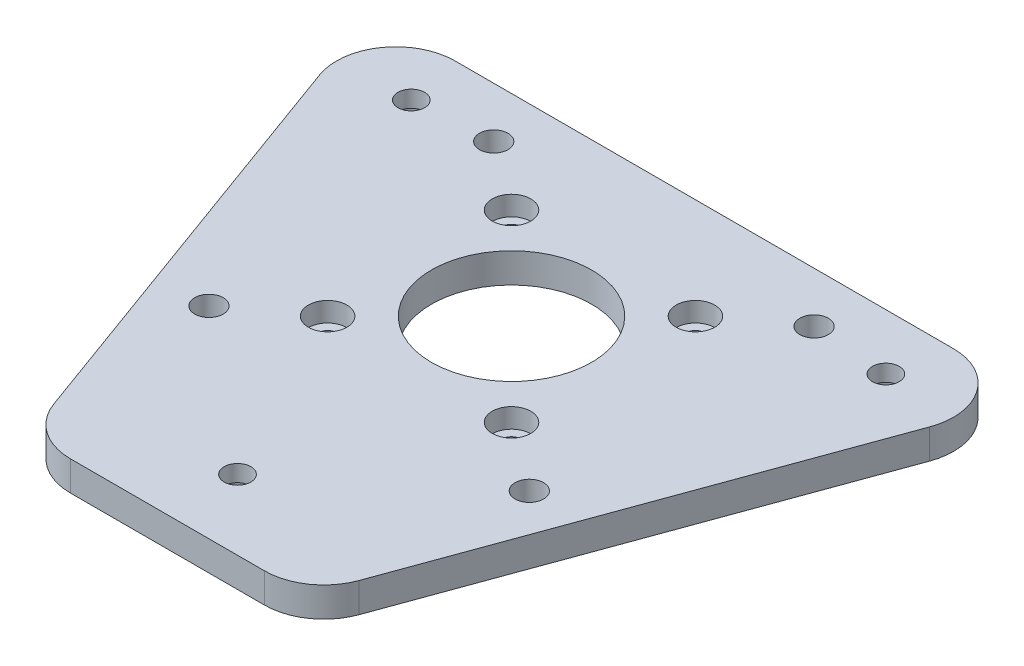
SolidWorks part; units mm, degrees
material "Nylon 101"
ref_plane "Front Plane" through (0, 0, 0) normal (0, 0, 1) x (1, 0, 0)
ref_plane "Top Plane" through (0, 0, 0) normal (0, 1, 0) x (1, 0, 0)
ref_plane "Right Plane" through (0, 0, 0) normal (1, 0, 0) x (0, 0, -1)
sketch "Sketch2" plane through (0, 0, 0) normal (0, 1, 0) x (1, 0, 0)
  line L1 (-65, -65) -> (65, -65)
  line L2 (-65, -65) -> (-65, 65)
  line L3 (-65, 65) -> (65, 65)
  line L4 (65, -65) -> (65, 65)
  line L5 (-65, -65) -> (65, 65) construction
  line L6 (-65, 65) -> (65, -65) construction
  point P0 (0, 0)
  dimension "D1" = 130
  dimension "D2" = 130
extrude "Boss-Extrude1" add sketch "Sketch2" along normal blind 5
ref_plane "Plane1" through (0, 5, 0) normal (0, 1, 0) x (1, 0, 0)
sketch "Sketch3" plane through (0, 5, 0) normal (0, 1, 0) x (1, 0, 0)
  line L0 (0, 0) -> (0, 15.5) construction
  line L1 (0, 15.5) -> (-15.5, 15.5) construction
  line L2 (0, 0) -> (-27, 0) construction
  line L3 (0, 0) -> (0, -24) construction
  circle A0 centre (0, 0) radius 13.5
  point P17 (-27, -24)
  point P18 (27, -24)
  point P25 (15.5, -15.5)
  point P26 (-15.5, -15.5)
  point P27 (-15.5, 15.5)
  point P28 (-27, 24)
  point P29 (27, 24)
  point P30 (15.5, 15.5)
  dimension "D1" = 27
  dimension "D4" = 15.5
  dimension "D9" = 15.5
  dimension "D2" = 15.5
  dimension "D3" = 15.5
  dimension "D6" = 27
  dimension "D7" = 54
  dimension "D8" = 24
  dimension "D5" = 48
  dimension "D10" = 27
  dimension "D11" = 24
extrude "Cut-Extrude1" cut sketch "Sketch3" against normal blind 5
ref_plane "Plane3" through (0, 5, 0) normal (0, 1, 0) x (1, 0, 0)
sketch "Sketch5" plane through (0, 0, 0) normal (0, 1, 0) x (1, 0, 0)
  line L0 (0, 0) -> (-40, 0) construction
  line L1 (-40, 0) -> (-40, 23.1) construction
  line L2 (0, 0) -> (0, -18.9982) construction
  point P11 (0, -46.19)
  point P12 (-40, 23.1)
  point P13 (40, 23.1)
  dimension "D3" = 46.19
  dimension "D1" = 23.1
  dimension "D2" = 40
  dimension "D4" = 40
ref_plane "Plane6" through (0, 5, 0) normal (0, 1, 0) x (1, 0, 0)
sketch "Sketch8" plane through (0, 5, 0) normal (0, 1, 0) x (1, 0, 0)
  line L0 (0, 0) -> (0, 30.6481) construction
  line L1 (0, 0) -> (56.2917, 32.5) construction
  line L2 (0, 0) -> (37.3839, 0) construction
  line L3 (0, 0) -> (-56.2917, 32.5) construction
  line L4 (0, 0) -> (0, -58) construction
  line L5 (-42.0098, 32.5) -> (42.0098, 32.5)
  line L6 (51.4067, 19.0796) -> (25.7449, -51.4204)
  line L7 (-51.4067, 19.0796) -> (-25.7449, -51.4204)
  line L8 (-16.3481, -58) -> (16.3481, -58)
  line L9 (-65, 65) -> (-65, -65)
  line L10 (-65, -65) -> (65, -65)
  line L11 (65, -65) -> (65, 65)
  line L12 (65, 65) -> (-65, 65)
  arc A0 (-25.7449, -51.4204) -> (-16.3481, -58) centre (-16.3481, -48) ccw
  arc A1 (25.7449, -51.4204) -> (16.3481, -58) centre (16.3481, -48) cw
  arc A2 (51.4067, 19.0796) -> (42.0098, 32.5) centre (42.0098, 22.5) ccw
  arc A3 (-51.4067, 19.0796) -> (-42.0098, 32.5) centre (-42.0098, 22.5) cw
  point P9 (0, -58)
  point P14 (-23.35, -58)
  point P17 (23.35, -58)
  dimension "D5" = 10
  dimension "D1" = 30
  dimension "D2" = 65
  dimension "D3" = 58
  dimension "D4" = 46.7
extrude "Cut-Extrude6" cut sketch "Sketch8" against normal through all
hole_wizard "M4 Clearance Hole1" positions "Sketch11" profile "Sketch12" hole size "M4" standard "ANSI Metric" end condition up to next
sketch "Sketch11" plane through (0, 5, 0) normal (0, 1, 0) x (1, 0, 0)
  point P0 (-27, 24)
  point P4 (27, 24)
  point P7 (27, -24)
  point P10 (-27, -24)
sketch "Sketch12" plane through (-27, 5, -24) normal (1, 0, 0) x (0, 0, 1)
  line L0 (0, 0) -> (0, 5)
  line L1 (0, 5) -> (2.4, 5)
  line L2 (2.4, 5) -> (2.4, 0)
  line L5 (2.4, 0) -> (0, 0)
  line L11 (0, -6.35) -> (0, 107.95) construction
  dimension "Thru Hole Dia." = 4.8
  dimension "Thru Hole Depth" = 5
hole_wizard "CBORE for M3 Hex Head Machine Screw1" positions "Sketch15" profile "Sketch16" counterbore size "M3" standard "ANSI Metric" end condition up to next
sketch "Sketch15" plane through (0, 5, 0) normal (0, 1, 0) x (1, 0, 0)
  point P0 (-15.5, 15.5)
  point P3 (15.5, 15.5)
  point P6 (15.5, -15.5)
  point P9 (-15.5, -15.5)
sketch "Sketch16" plane through (-15.5, 5, -15.5) normal (1, 0, 0) x (0, 0, 1)
  line L0 (0, 0) -> (0, 5)
  line L1 (0, 5) -> (1.7, 5)
  line L3 (1.7, 5) -> (1.7, 3.3)
  line L4 (1.7, 3.3) -> (3.25, 3.3)
  line L5 (3.25, 3.3) -> (3.25, 0)
  line L7 (3.25, 0) -> (0, 0)
  line L11 (0, -6.35) -> (0, 107.95) construction
  dimension "Thru Hole Dia." = 3.4
  dimension "Thru Hole Depth" = 5
  dimension "C'Bore Dia." = 6.5
  dimension "C'Bore Depth" = 3.3
hole_wizard "CBORE for M4 SBHCS1" positions "Sketch18" profile "Sketch19" counterbore size "M4" standard "ANSI Metric" end condition up to next
sketch "Sketch18" plane through (0, 0, 0) normal (0, -1, 0) x (-1, 0, 0)
  point P0 (0, -46.19)
  point P3 (40, 23.1)
  point P6 (-40, 23.1)
sketch "Sketch19" plane through (0, 0, 46.19) normal (1, 0, 0) x (0, 0, -1)
  line L0 (0, 0) -> (0, 5)
  line L1 (0, 5) -> (2.25, 5)
  line L3 (2.25, 5) -> (2.25, 2.2)
  line L4 (2.25, 2.2) -> (4.3, 2.2)
  line L5 (4.3, 2.2) -> (4.3, 0)
  line L7 (4.3, 0) -> (0, 0)
  line L11 (0, -6.35) -> (0, 107.95) construction
  dimension "Thru Hole Dia." = 4.5
  dimension "Thru Hole Depth" = 5
  dimension "C'Bore Dia." = 8.6
  dimension "C'Bore Depth" = 2.2
